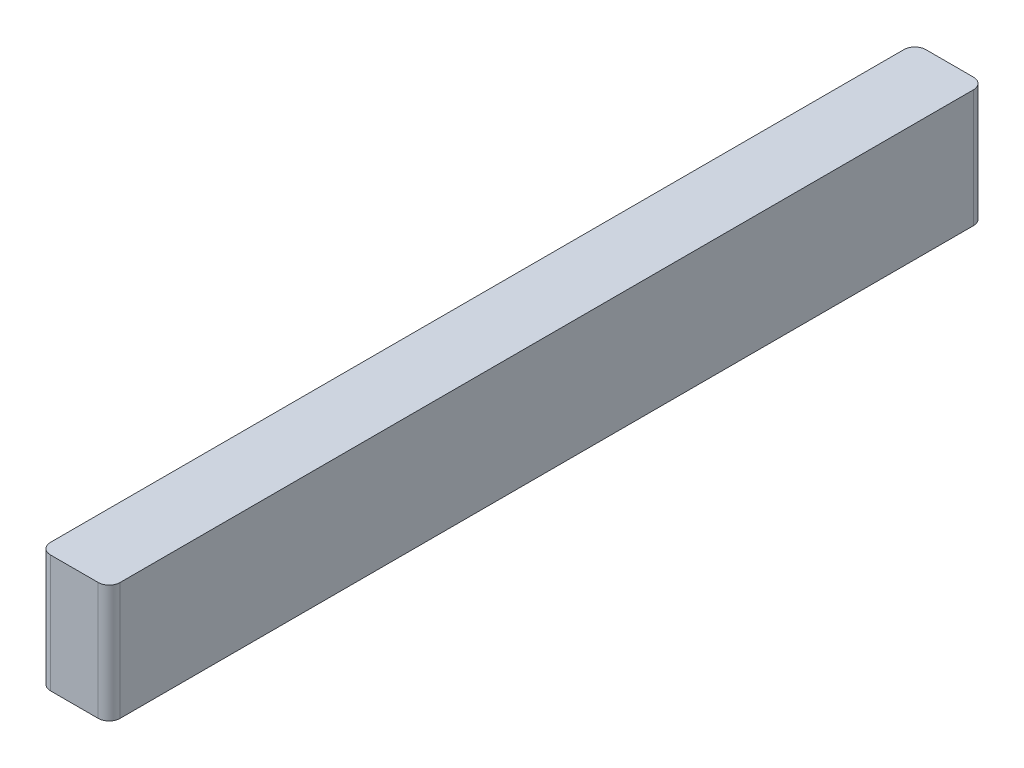
SolidWorks part; units mm, degrees
ref_plane "Front Plane" through (0, 0, 0) normal (0, 0, 1) x (1, 0, 0)
ref_plane "Top Plane" through (0, 0, 0) normal (0, 1, 0) x (1, 0, 0)
ref_plane "Right Plane" through (0, 0, 0) normal (1, 0, 0) x (0, 0, -1)
sketch "Sketch1" plane through (0, 0, 0) normal (0, 1, 0) x (1, 0, 0)
  line L1 (6.35, 0) -> (34.036, 0)
  line L2 (0, 6.35) -> (0, 501.65)
  line L3 (6.35, 508) -> (34.036, 508)
  line L4 (40.386, 6.35) -> (40.386, 501.65)
  arc A0 (34.036, 0) -> (40.386, 6.35) centre (34.036, 6.35) ccw
  arc A1 (6.35, 0) -> (0, 6.35) centre (6.35, 6.35) cw
  arc A2 (34.036, 508) -> (40.386, 501.65) centre (34.036, 501.65) cw
  arc A3 (0, 501.65) -> (6.35, 508) centre (6.35, 501.65) cw
  point P7 (40.386, 0)
  point P10 (0, 0)
  point P15 (0, 508)
  dimension "D3" = 6.35
  dimension "D1" = 40.386
  dimension "D2" = 508
extrude "Boss-Extrude1" add sketch "Sketch1" along normal blind 68.326
